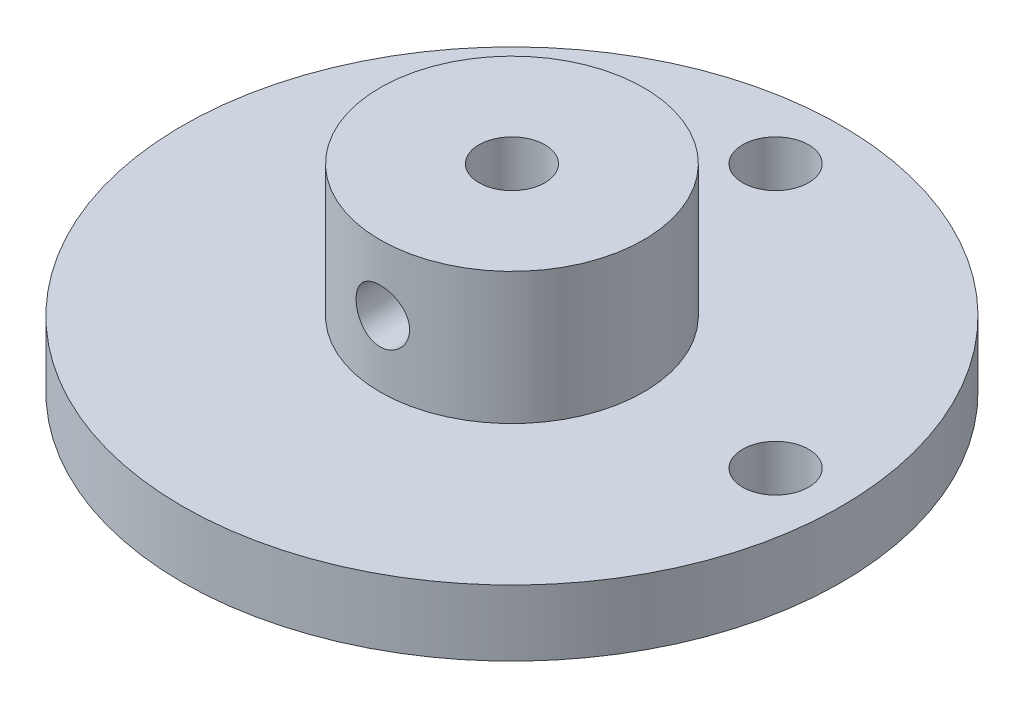
SolidWorks part; units mm, degrees
material "1060 Alloy"
ref_plane "Front Plane" through (0, 0, 0) normal (0, 0, 1) x (1, 0, 0)
ref_plane "Top Plane" through (0, 0, 0) normal (0, 1, 0) x (1, 0, 0)
ref_plane "Right Plane" through (0, 0, 0) normal (1, 0, 0) x (0, 0, -1)
sketch "Sketch1" plane through (0, 0, 0) normal (0, 1, 0) x (1, 0, 0)
  line L0 (15.875, 0) -> (0, 0) construction
  line L1 (0, 0) -> (0, 15.875) construction
  circle A0 centre (0, 0) radius 15.875
  circle A1 centre (0, 12.7) radius 1.5875
  circle A2 centre (12.7, 0) radius 1.5875
  dimension "D1" = 31.75
  dimension "D2" = 3.175
  dimension "D3" = 3.175
  dimension "D4" = 12.7
  dimension "D5" = 12.7
extrude "Boss-Extrude1" add sketch "Sketch1" along normal blind 3.175
sketch "Sketch2" plane through (0, 3.175, 0) normal (0, 1, 0) x (1, 0, 0)
  circle A0 centre (0, 0) radius 6.35
  dimension "D1" = 12.7
extrude "Boss-Extrude2" add sketch "Sketch2" along normal blind 6.35
sketch "Sketch3" plane through (0, 9.525, 0) normal (0, 1, 0) x (1, 0, 0)
  circle A0 centre (0, 0) radius 1.5875
  dimension "D1" = 3.175
extrude "Cut-Extrude1" cut sketch "Sketch3" against normal through all
hole_wizard "#38 (0.1015) Diameter Hole1" positions "Sketch6" profile "Sketch5" hole size "#38" standard "ANSI Inch"
sketch "Sketch6" plane through (0, 0, 0) normal (0, 0, 1) x (1, 0, 0)
  line L0 (0, 0) -> (0, 9.525) construction
  line L1 (6.35, 9.525) -> (-6.35, 9.525) construction
  line L2 (1.5875, 9.525) -> (-1.5875, 9.525) construction
  point P10 (0, 6.35)
  dimension "D1" = 3.175
sketch "Sketch5" plane through (0, 6.35, 0) normal (1, 0, 0) x (0, 1, 0)
  line L0 (0, 0) -> (0, 26.1745)
  line L1 (0, 26.1745) -> (1.289, 25.4)
  line L2 (1.289, 25.4) -> (1.289, 0)
  line L5 (1.289, 0) -> (0, 0)
  line L10 (0, 26.1745) -> (-1.2891, 25.4) construction
  line L11 (0, -6.35) -> (0, 107.95) construction
  dimension "Hole Dia." = 2.5781
  dimension "Hole Depth" = 25.4
  dimension "Drill Angle" = 118
